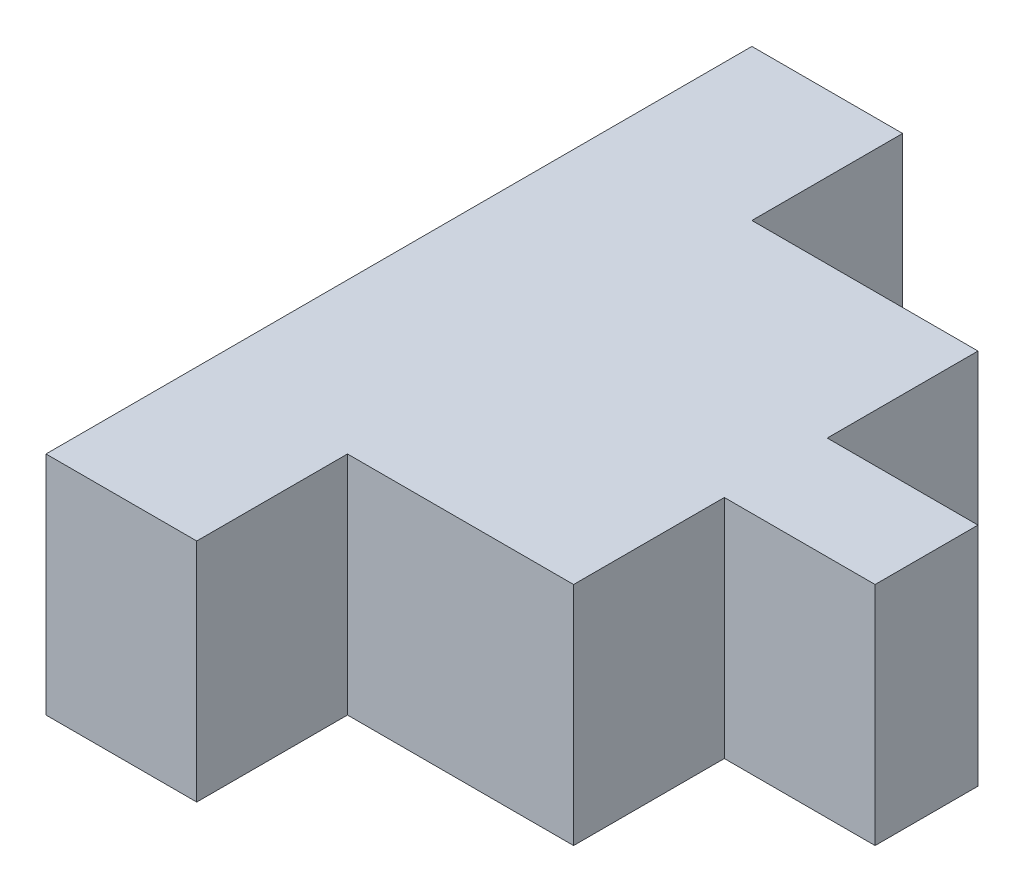
SolidWorks part; units mm, degrees
ref_plane "Front Plane" through (0, 0, 0) normal (0, 0, 1) x (1, 0, 0)
ref_plane "Top Plane" through (0, 0, 0) normal (0, 1, 0) x (1, 0, 0)
ref_plane "Right Plane" through (0, 0, 0) normal (1, 0, 0) x (0, 0, -1)
sketch "Sketch3" plane through (0, 0, 0) normal (0, 1, 0) x (1, 0, 0)
  line L0 (0, 0) -> (50.8, 0)
  line L1 (50.8, 0) -> (50.8, 50.8)
  line L2 (50.8, 50.8) -> (127, 50.8)
  line L3 (127, 50.8) -> (127, 101.6)
  line L4 (127, 101.6) -> (177.8, 101.6)
  line L5 (177.8, 101.6) -> (177.8, 136.2852)
  line L6 (177.8, 118.9426) -> (-4.0266, 118.9426) construction
  line L7 (127, 136.2852) -> (177.8, 136.2852)
  line L8 (127, 187.0852) -> (127, 136.2852)
  line L9 (50.8, 187.0852) -> (127, 187.0852)
  line L10 (50.8, 237.8852) -> (50.8, 187.0852)
  line L11 (0, 237.8852) -> (50.8, 237.8852)
  line L12 (0, 237.8852) -> (0, 0)
extrude "Boss-Extrude1" add sketch "Sketch3" along normal blind 76.2
